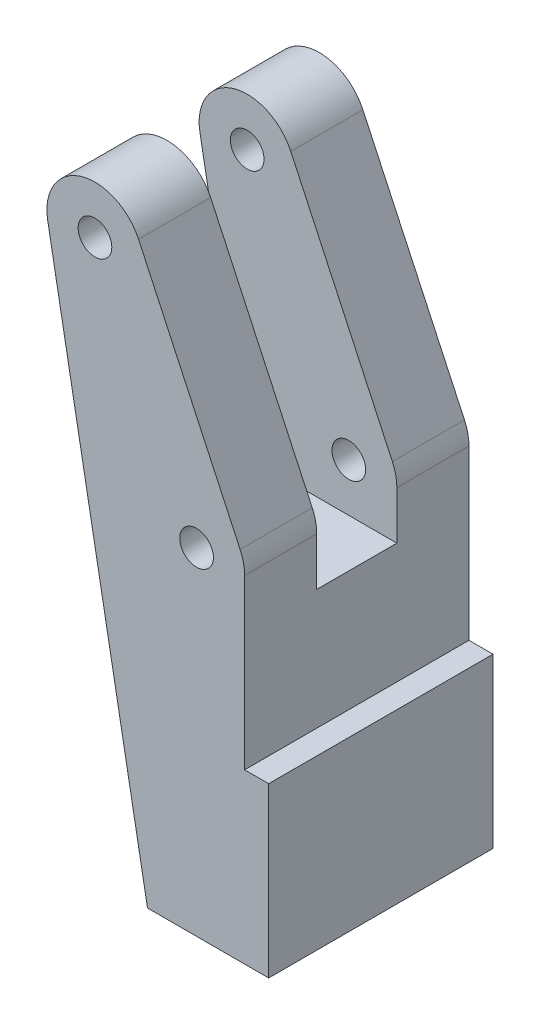
SolidWorks part; units mm, degrees
ref_plane "Front Plane" through (0, 0, 0) normal (0, 0, 1) x (1, 0, 0)
ref_plane "Top Plane" through (0, 0, 0) normal (0, 1, 0) x (1, 0, 0)
ref_plane "Right Plane" through (0, 0, 0) normal (1, 0, 0) x (0, 0, -1)
sketch "Sketch1" plane through (0, 0, 0) normal (0, 0, 1) x (1, 0, 0)
  line L0 (0, 0) -> (0, -35) construction
  line L1 (0, 0) -> (-10.5655, 22.6577) construction
  line L2 (-6.0339, 24.7708) -> (4.5315, 2.1131)
  line L3 (5, 0) -> (5, -35)
  line L4 (-5.1029, -35) -> (-15.4839, 21.7581)
  line L5 (5, -35) -> (-5.1029, -35)
  arc A1 (5, 0) -> (4.5315, 2.1131) centre (0, 0) ccw
  arc A2 (-6.0339, 24.7708) -> (-15.4839, 21.7581) centre (-10.5655, 22.6577) ccw
  circle A3 centre (-10.5655, 22.6577) radius 1.75
  circle A4 centre (0, 0) radius 1.75
  dimension "D4" = 10
  dimension "D5" = 10
  dimension "D7" = 3.5
  dimension "D8" = 3.5
  dimension "D1" = 25
  dimension "D2" = 25
  dimension "D3" = 35
extrude "Boss-Extrude1" add sketch "Sketch1" along normal blind 7.5
sketch "Sketch2" plane through (0, 0, 7.5) normal (0, 0, 1) x (1, 0, 0)
  line L0 (5, -5) -> (-10.5898, -5)
  line L1 (5, -35) -> (5, 0) construction
  line L2 (-15.4839, 21.7581) -> (-5.1029, -35) construction
  line L3 (-10.5898, -5) -> (-5.1029, -35)
  line L4 (-5.1029, -35) -> (5, -35)
  line L5 (5, -35) -> (5, -5)
  circle A0 centre (0, 0) radius 5 construction
  dimension "D1" = 10
extrude "Boss-Extrude2" add sketch "Sketch2" along normal blind 8.3333
sketch "Sketch3" plane through (0, 0, 15.8333) normal (0, 0, 1) x (1, 0, 0)
  line L0 (5, 0) -> (5, -35)
  line L1 (5, -35) -> (-5.1029, -35)
  line L2 (-5.1029, -35) -> (-15.4839, 21.7581)
  line L3 (-6.0339, 24.7708) -> (4.5315, 2.1131)
  arc A0 (-15.4839, 21.7581) -> (-6.0339, 24.7708) centre (-10.5655, 22.6577) cw
  arc A1 (5, 0) -> (4.5315, 2.1131) centre (0, 0) ccw
  circle A2 centre (0, 0) radius 1.75
  circle A3 centre (-10.5655, 22.6577) radius 1.75
extrude "Boss-Extrude4" add sketch "Sketch3" along normal blind 7.5
sketch "Sketch4" plane through (5, 0, 0) normal (1, 0, 0) x (0, 0, -1)
  line L0 (0, -35) -> (-23.3333, -35)
  line L1 (-23.3333, -35) -> (-23.3333, -17.5)
  line L2 (-23.3333, -35) -> (-23.3333, 0) construction
  line L3 (-23.3333, -17.5) -> (0, -17.5)
  line L4 (0, -35) -> (0, 0) construction
  line L5 (0, -17.5) -> (0, -35)
extrude "Boss-Extrude5" add sketch "Sketch4" along normal blind 2.5
